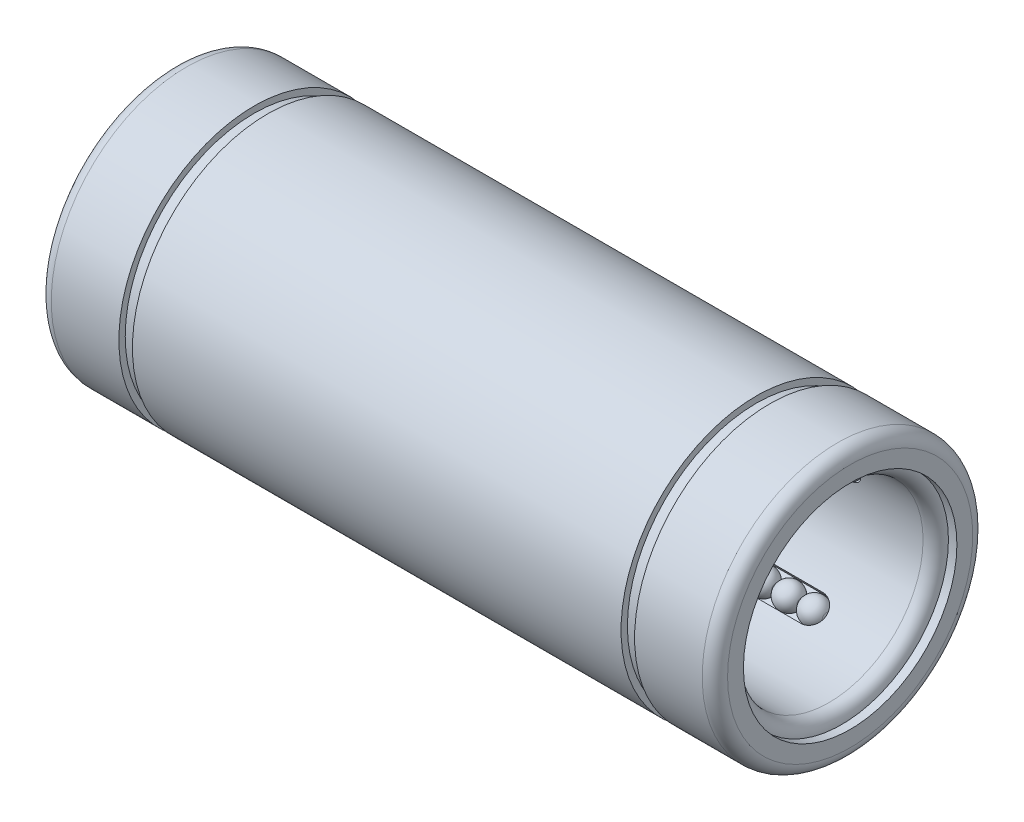
SolidWorks part; units mm, degrees
ref_plane "Спереди" through (0, 0, 0) normal (0, 0, 1) x (1, 0, 0)
ref_plane "Сверху" through (0, 0, 0) normal (0, 1, 0) x (1, 0, 0)
ref_plane "Слева" through (0, 0, 0) normal (1, 0, 0) x (0, 0, -1)
sketch "Эскиз1" plane through (0, 0, 0) normal (0, 0, 1) x (1, 0, 0)
  line L0 (0, 0) -> (-45.148, 0) construction
  line L1 (0, 0) -> (0, 20.831) construction
  line L2 (0, 16) -> (-28.9, 16)
  line L3 (-40, 16) -> (-40, 0)
  line L4 (-30.5, 16) -> (-40, 16)
  line L5 (-40, 10) -> (0, 10)
  line L6 (-30.5, 16) -> (-30.5, 15.25)
  line L7 (-30.5, 15.25) -> (-28.9, 15.25)
  line L8 (-28.9, 16) -> (-28.9, 15.25)
  line L9 (-30.5, 15.25) -> (-30.5, 3.2154) construction
  line L10 (-9.5, 14.0183) -> (-9.5, 5.6096) construction
  circle A0 centre (-29, 11.5) radius 1.5
  dimension "D7" = 3
  dimension "D1" = 80
  dimension "D2" = 32
  dimension "D3" = 1.6
  dimension "D4" = 61
  dimension "D5" = 30.5
  dimension "D6" = 20
  dimension "D8" = 9.5
  dimension "D9" = 9.5
  dimension "D10" = 21
sketch "Эскиз2" plane through (0, 0, 0) normal (0, 0, 1) x (1, 0, 0)
  line L0 (-30.5, 11.5) -> (-27.5, 11.5)
  line L1 (-27.5, 11.5) -> (-26.5586, 11.5) construction
  line L2 (-30.5, 11.5) -> (-30.5, 11.25)
  line L3 (-27.5, 11.5) -> (-27.5, 11.25)
  line L4 (-27.5811, 11.0135) -> (-27.5, 11.25)
  line L5 (-30.5, 11.25) -> (-30.4189, 11.0135)
  circle A0 centre (-29, 11.5) radius 1.5 construction
  arc A1 (-30.5, 11.5) -> (-27.5, 11.5) centre (-29, 11.5) ccw construction
  arc A2 (-30.4189, 11.0135) -> (-27.5811, 11.0135) centre (-29, 11.5) ccw
  dimension "D1" = 0.25
revolve "Повернуть1" add sketch "Эскиз2" angle 360 about L1
pattern_linear "Линейный массив1" count 7 spacing 3 along (1, 0, 0) of bodies 101
combine bodies "Соединить2" operation type add bodies to combine 101 102 103 104 105 106 107
pattern_circular "Круговой массив1" count 5 over 360 about axis through (0, 0, 0) along (1, 0, 0) of bodies 177 107 106 105 104 103 102 101
sketch "Эскиз3" plane through (0, 0, 0) normal (0, 0, 1) x (1, 0, 0)
  line L0 (0, 0) -> (0, 20.831) construction
  line L1 (-39, 15.25) -> (-38.25, 15.25)
  line L2 (-39, 15.25) -> (-39, 12.625)
  line L3 (0, 0) -> (-29.7228, 0) construction
  line L4 (-38.25, 15.25) -> (-38.25, 12.625)
  line L5 (-37.5, 11.125) -> (0, 11.125)
  line L6 (-30.5, 16) -> (-40, 16) construction
  line L7 (-37.5, 11.875) -> (0, 11.875)
  line L8 (0, 11.125) -> (0, 11.875)
  line L9 (-29, 11.5) -> (0, 11.5) construction
  line L10 (-40, 16) -> (-40, 0) construction
  line L11 (0, 0) -> (-45.148, 0) construction
  arc A0 (-38.25, 12.625) -> (-37.5, 11.875) centre (-37.5, 12.625) ccw
  arc A1 (-37.5, 11.125) -> (-39, 12.625) centre (-37.5, 12.625) cw
  dimension "D4" = 0.75
  dimension "D5" = 1.5
  dimension "D1" = 0.75
  dimension "D2" = 0.75
  dimension "D3" = 1
revolve "Повернуть2" add sketch "Эскиз3" angle 360 about L0
sketch "Эскиз4" plane through (0, 0, 0) normal (0, 1, 0) x (1, 0, 0)
  line L0 (0, 0) -> (-45.148, 0) construction
  line L1 (-29, 1.6) -> (-11, 1.6)
  line L2 (-29, -1.6) -> (-11, -1.6)
  arc A0 (-29, 1.6) -> (-29, -1.6) centre (-29, 0) ccw
  arc A1 (-11, -1.6) -> (-11, 1.6) centre (-11, 0) ccw
  dimension "D1" = 3.2
  dimension "D2" = 18
extrude "Вытянуть1" cut sketch "Эскиз4" along normal through all
pattern_circular "Круговой массив2" count 5 over 360 about axis through (0, 0, 0) along (1, 0, 0) of "Вытянуть1"
sketch "Эскиз5" plane through (0, 0, 0) normal (0, 0, 1) x (1, 0, 0)
  line L0 (-39, 12.625) -> (-40, 12.625)
  line L1 (-40, 16) -> (-40, 0) construction
  line L2 (-40, 12.625) -> (-40, 14.5)
  line L3 (-38.5, 16) -> (-30.5, 16)
  line L4 (-30.5, 16) -> (-30.5, 15.25)
  line L5 (-30.5, 15.25) -> (-28.9, 15.25)
  line L6 (-28.9, 15.25) -> (-28.9, 16)
  line L7 (-28.9, 16) -> (0, 16)
  line L8 (0, 16) -> (0, 11.875)
  line L9 (0, 11.875) -> (-9.0355, 11.875)
  line L10 (-11, 13.5) -> (-29, 13.5)
  line L11 (-37.5, 11.875) -> (0, 11.875) construction
  line L12 (-38.25, 15.25) -> (-38.25, 12.625) construction
  line L13 (-39, 15.25) -> (-38.25, 15.25) construction
  line L14 (-39, 15.25) -> (-39, 12.625) construction
  line L15 (-37.5, 11.875) -> (-30.9645, 11.875)
  line L16 (-38.25, 15.25) -> (-38.25, 12.625)
  line L17 (-39, 15.25) -> (-38.25, 15.25)
  line L18 (-39, 15.25) -> (-39, 12.625)
  line L19 (-12.9645, 11.875) -> (0, 11.875)
  arc A1 (-9.0355, 11.875) -> (-11, 13.5) centre (-11, 11.5) ccw
  circle A2 centre (-29, 11.5) radius 2
  arc A3 (-29, 13.5) -> (-30.9645, 11.875) centre (-29, 11.5) ccw
  arc A4 (-38.25, 12.625) -> (-37.5, 11.875) centre (-37.5, 12.625) ccw construction
  arc A5 (-38.25, 12.625) -> (-37.5, 11.875) centre (-37.5, 12.625) ccw
  arc A6 (-38.5, 16) -> (-40, 14.5) centre (-38.5, 14.5) ccw
  point P34 (-40, 16)
  dimension "D2" = 18
  dimension "D3" = 1.5
  dimension "D1" = 0.5
revolve "Повернуть3" add sketch "Эскиз5" angle 360 about L0
mirror "Зеркальное отражение4" about plane through (0, -17.4816, 0) normal (-1, 0, 0) of bodies 177 108 109 110 111
mirror "Зеркальное отражение5" about plane through (0, -17.4816, 0) normal (-1, 0, 0) of bodies 138 139
